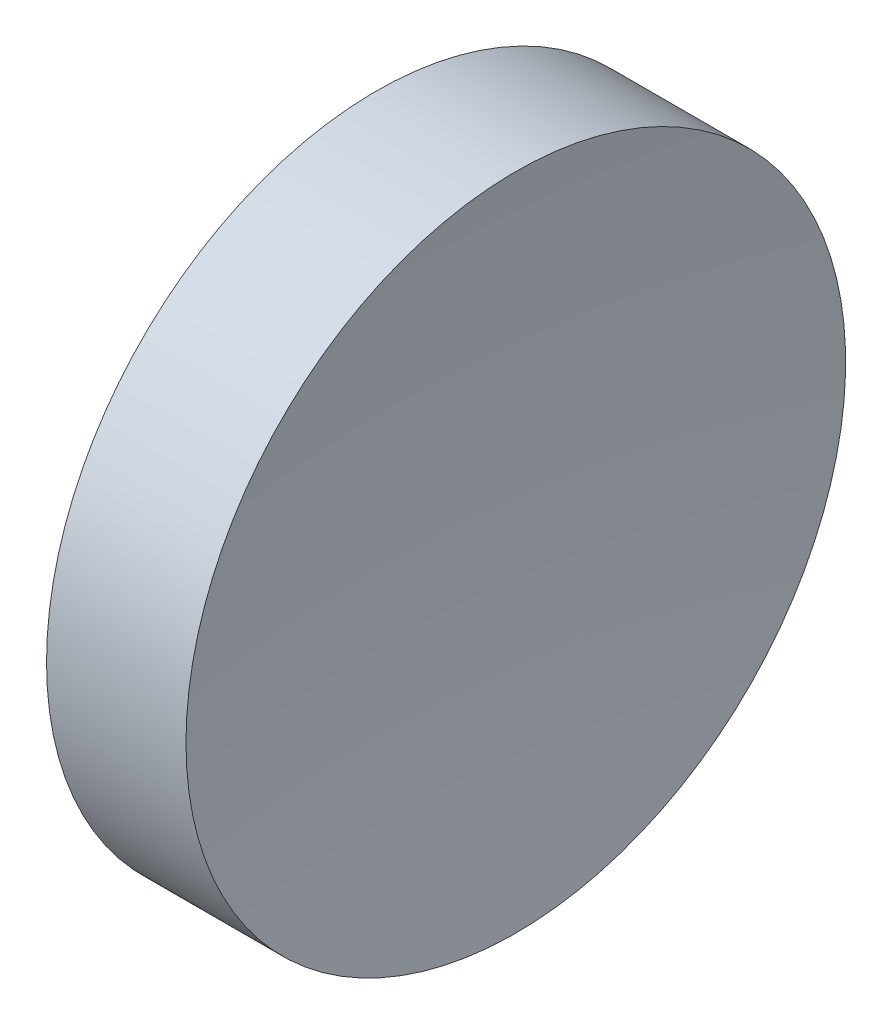
SolidWorks part; units mm, degrees
ref_plane "前视基准面" through (0, 0, 0) normal (0, 0, 1) x (1, 0, 0)
ref_plane "上视基准面" through (0, 0, 0) normal (0, 1, 0) x (1, 0, 0)
ref_plane "右视基准面" through (0, 0, 0) normal (1, 0, 0) x (0, 0, -1)
sketch "草图1" plane through (0, 0, 0) normal (0, 0, 1) x (1, 0, 0)
  line L0 (217.9703, 138.756) -> (265.5527, 138.756) construction
  line L1 (230.1853, 138.756) -> (230.1853, 163.756)
  line L2 (239.1853, 138.756) -> (230.1853, 138.756)
  line L3 (230.1853, 163.756) -> (240.754, 163.756)
  arc A0 (240.754, 163.756) -> (239.1853, 138.756) centre (439.1853, 138.756) ccw
  dimension "D2" = 200
  dimension "D1" = 10.5687
revolve "旋转1" add sketch "草图1" angle 360 about L0
